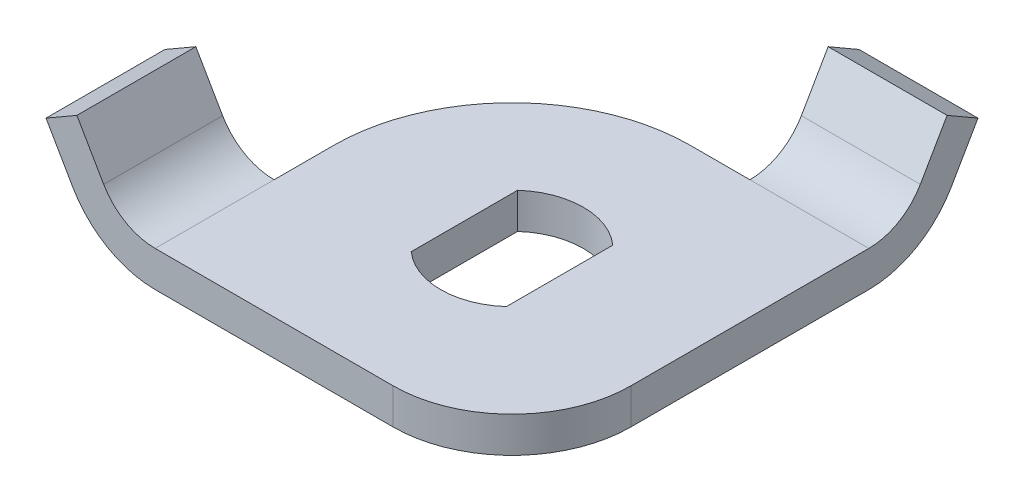
SolidWorks part; units mm, degrees
ref_plane "Front Plane" through (0, 0, 0) normal (0, 0, 1) x (1, 0, 0)
ref_plane "Top Plane" through (0, 0, 0) normal (0, 1, 0) x (1, 0, 0)
ref_plane "Right Plane" through (0, 0, 0) normal (1, 0, 0) x (0, 0, -1)
sketch "Sketch1" plane through (0, 0, 0) normal (0, 1, 0) x (1, 0, 0)
  line L1 (-15, -15) -> (15, -15)
  line L2 (-15, -15) -> (-15, 15)
  line L3 (-15, 15) -> (15, 15)
  line L4 (15, -15) -> (15, 15)
  line L5 (-15, -15) -> (15, 15) construction
  line L6 (-15, 15) -> (15, -15) construction
  point P0 (0, 0)
  dimension "D1" = 30
  dimension "D2" = 30
extrude "Boss-Extrude1" add sketch "Sketch1" along normal blind 3
sketch "Sketch2" plane through (0, 0, 15) normal (0, 0, 1) x (1, 0, 0)
  line L0 (-24.1782, 7.8971) -> (-21.9282, 4)
  line L1 (-21.5801, 9.3971) -> (-19.3301, 5.5)
  line L2 (-24.1782, 7.8971) -> (-21.5801, 9.3971)
  line L3 (-15, 0) -> (15, 0) construction
  line L4 (-15, 3) -> (-15, 0)
  line L5 (-15, 3) -> (15, 3) construction
  arc A0 (-19.3301, 5.5) -> (-15, 3) centre (-15, 8) ccw
  arc A1 (-21.9282, 4) -> (-15, 0) centre (-15, 8) ccw
  line M7 (-15, 3) -> (-15, 0)
  dimension "D1" = 5
  dimension "D2" = 60
  dimension "D3" = 4.5
extrude "Boss-Extrude2" add sketch "Sketch2" against normal blind 10 contours L0 A1 A0 L1 L2 M7
fillet "Fillet1" radius 15 1 edges at (-15, 1.5, -15)
fillet "Fillet2" radius 10 1 edges at (15, 1.5, 15)
sketch "Sketch3" plane through (15, 0, 0) normal (1, 0, 0) x (0, 0, -1)
  line L0 (15, 3) -> (15, 0)
  line L1 (-5, 3) -> (15, 3) construction
  line L2 (-5, 0) -> (15, 0) construction
  line L3 (19.3301, 5.5) -> (21.5801, 9.3971)
  line L4 (21.5801, 9.3971) -> (24.1782, 7.8971)
  line L5 (24.1782, 7.8971) -> (21.9282, 4)
  arc A0 (15, 3) -> (19.3301, 5.5) centre (15, 8) ccw
  arc A1 (15, 0) -> (21.9282, 4) centre (15, 8) ccw
  dimension "D1" = 5
  dimension "D2" = 4.5
  dimension "D3" = 60
extrude "Boss-Extrude3" add sketch "Sketch3" against normal blind 10
sketch "Sketch4" plane through (0, 0, 0) normal (0, -1, 0) x (1, 0, 0)
  line L0 (-4, -4.4721) -> (-4, 4.4721)
  line L2 (4, 4.4721) -> (4, -4.4721)
  arc A0 (-4, -4.4721) -> (4, -4.4721) centre (0, 0) ccw
  arc A1 (4, 4.4721) -> (-4, 4.4721) centre (0, 0) ccw
  dimension "D1" = 6
  dimension "D2" = 8
  dimension "D3" = 4
extrude "Cut-Extrude1" cut sketch "Sketch4" against normal up to surface (3 mm away) up to face at (-0.7544, 3, -1.6919)
